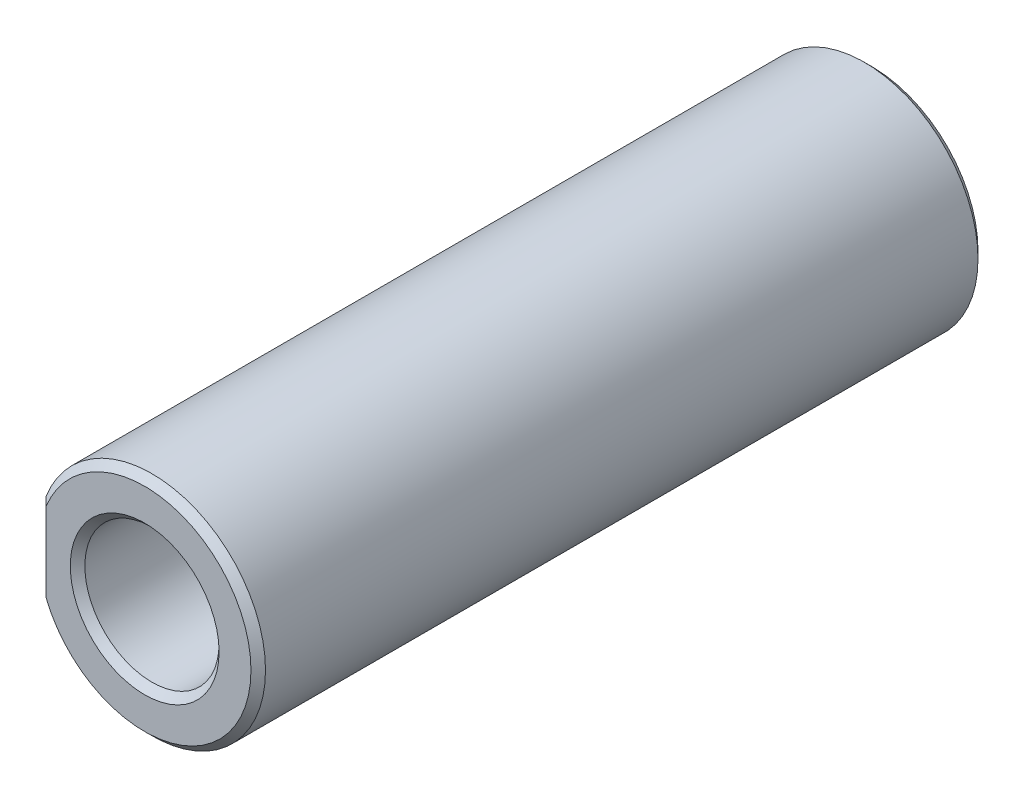
SolidWorks part; units mm, degrees
ref_plane "Front Plane" through (0, 0, 0) normal (0, 0, 1) x (1, 0, 0)
ref_plane "Top Plane" through (0, 0, 0) normal (0, 1, 0) x (1, 0, 0)
ref_plane "Right Plane" through (0, 0, 0) normal (1, 0, 0) x (0, 0, -1)
sketch "Sketch1" plane through (0, 0, 0) normal (0, 0, 1) x (1, 0, 0)
  circle A0 centre (0, 0) radius 5.95
  dimension "D1" = 11.9
extrude "Boss-Extrude1" add sketch "Sketch1" along normal blind 38.1
sketch "Sketch2" plane through (0, 0, 0) normal (0, 0, -1) x (-1, 0, 0)
  circle A0 centre (0, 0) radius 3.175
  dimension "D1" = 6.35
extrude "Boss-Extrude2" add sketch "Sketch2" along normal blind 1.5875
hole_wizard "J (0.277) Diameter Hole1" positions "Sketch14" profile "Sketch16" hole size "J" standard "ANSI Inch"
sketch "Sketch14" plane through (0, 0, 38.1) normal (0, 0, 1) x (1, 0, 0)
  point P0 (0, 0)
sketch "Sketch16" plane through (0, 0, 38.1) normal (1, 0, 0) x (0, -1, 0)
  line L0 (0, 0) -> (0, 30.6888)
  line L1 (0, 30.6888) -> (3.5179, 28.575)
  line L2 (3.5179, 28.575) -> (3.5179, 0)
  line L5 (3.5179, 0) -> (0, 0)
  line L10 (0, 30.6888) -> (-3.5179, 28.575) construction
  line L11 (0, -6.35) -> (0, 107.95) construction
  dimension "Hole Dia." = 7.0358
  dimension "Hole Depth" = 28.575
  dimension "Drill Angle" = 118
hole_wizard "#8-32 Tapped Hole2" positions "Sketch17" profile "Sketch19" tap size "#8-32" standard "ANSI Inch" end condition through all
sketch "Sketch17" plane through (0, 0, -1.5875) normal (0, 0, -1) x (-1, 0, 0)
  point P0 (0, 0)
cosmetic thread "Hole Thread2" parameters "D2"=4.1656
sketch "Sketch19" plane through (0, 0, -1.5875) normal (1, 0, 0) x (0, 1, 0)
  line L0 (0, 0) -> (0, 39.6875)
  line L1 (0, 39.6875) -> (1.7272, 39.6875)
  line L2 (1.7272, 39.6875) -> (1.7272, 0)
  line L5 (1.7272, 0) -> (0, 0)
  line L11 (0, -6.35) -> (0, 107.95) construction
  dimension "Thru Tap Drill Dia." = 3.4544
  dimension "Thru Tap Drill Depth" = 39.6875
sketch "Sketch10" plane through (0, 0, 38.1) normal (0, 0, 1) x (1, 0, 0)
  line L0 (-5.5531, -2.1367) -> (-5.5531, 2.1367)
  circle A0 centre (0, 0) radius 5.95 construction
  point P4 (-5.95, 0)
  point P6 (0, 0)
  dimension "D1" = 0.3969
ref_plane "Plane2" through (-5.5531, 0, 0) normal (1, 0, 0) x (0, 1, 0)
sketch "Sketch9" plane through (-5.5531, 0, 0) normal (-1, 0, 0) x (0, 0, 1)
  line L1 (38.1, 3) -> (0, 3)
  line L2 (38.1, 3) -> (38.1, -3)
  line L3 (38.1, -3) -> (0, -3)
  line L4 (0, 3) -> (0, -3)
  line L5 (38.1, 3) -> (0, -3) construction
  line L6 (38.1, -3) -> (0, 3) construction
  line L7 (38.1, -2.1367) -> (38.1, 2.1367) construction
  line L8 (0, 5.95) -> (0, -5.95) construction
  line L9 (38.1, -5.95) -> (38.1, 5.95) construction
  point P0 (19.05, 0)
  point P5 (1.524, 0)
  point P11 (38.1, 0)
  dimension "D3" = 6
  dimension "D4" = 36.576
extrude "Cut-Extrude3" cut sketch "Sketch9" along normal through all
chamfer "Chamfer1" distance 0.381 angle 45 7 edges at (5.95, 0, 38.1) (-3.175, 0, -1.5875) (5.95, 0, 0) (3.5179, 0, 38.1) (-1.7272, 0, -1.5875) (-5.5531, 0, 38.1) (-5.5531, 0, 0)
fillet "Fillet1" radius 0.3969 1 edges at (-3.175, 0, 0)
